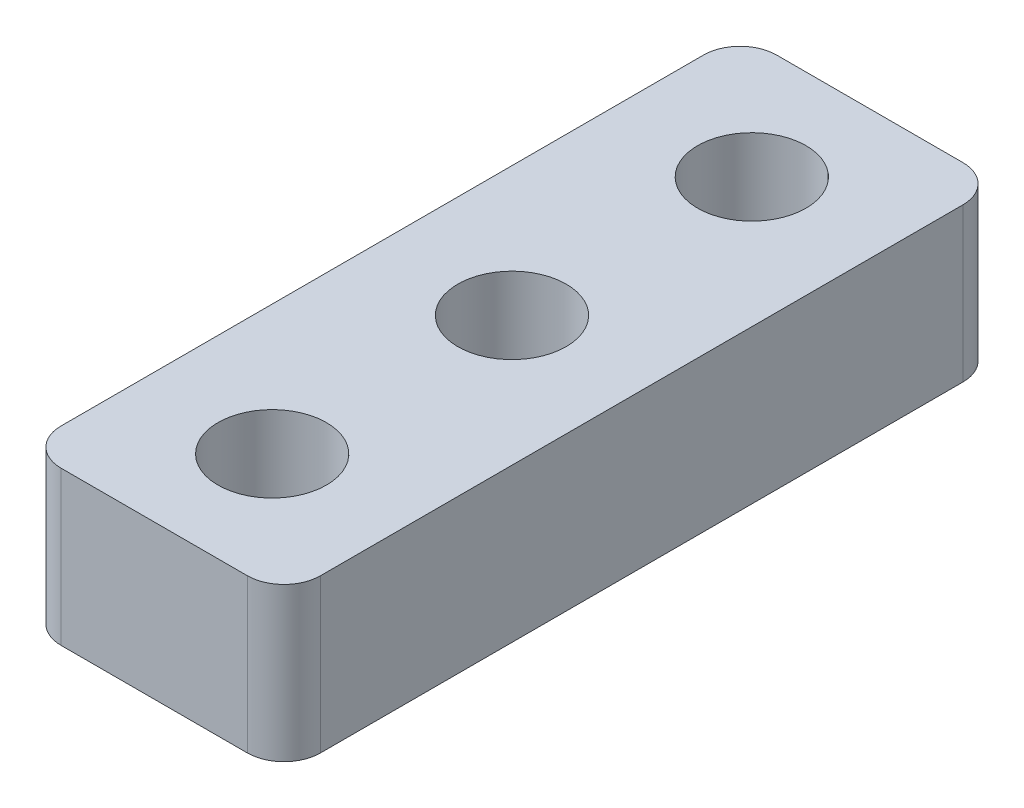
SolidWorks part; units mm, degrees
ref_plane "Front" through (0, 0, 0) normal (0, 0, 1) x (1, 0, 0)
ref_plane "Top" through (0, 0, 0) normal (0, 1, 0) x (1, 0, 0)
ref_plane "Right" through (0, 0, 0) normal (1, 0, 0) x (0, 0, -1)
sketch "Sketch1" plane through (0, 0, 0) normal (0, 0, 1) x (1, 0, 0)
  line L0 (0, 0) -> (0, 3.2004)
  line L1 (5.409, 3.7004) -> (0, 3.7004) construction
  line L2 (5.409, 3.7004) -> (5.409, 0) construction
  line L5 (2.7045, 3.7004) -> (2.7045, 0) construction
  line L10 (0, 3.2004) -> (5.409, 3.2004)
  line L15 (5.409, 3.7004) -> (5.409, 0) construction
  line L20 (0, 0) -> (5.409, 0)
  line L25 (5.409, 3.2004) -> (5.409, 0)
  line L30 (0, 3.7004) -> (0, 0) construction
  dimension "D1" = 5.409
  dimension "D2" = 3.2004
  dimension "D3" = 0.5
extrude "Boss-Extrude1" add sketch "Sketch1" along normal mid plane 14.92
sketch "Sketch3" plane through (0, 0, 0) normal (0, -1, 0) x (1, 0, 0)
  line L0 (0, 0) -> (5.409, 0) construction
  line L3 (0, 7.46) -> (0, -7.46) construction
  line L6 (2.7045, 5) -> (2.7045, -5) construction
  line L7 (5.409, 7.46) -> (5.409, -7.46) construction
  circle A0 centre (2.7045, 5) radius 1.1303
  circle A1 centre (2.7045, -5) radius 1.1303
  circle A2 centre (2.7045, 0) radius 1.1303
  point P8 (2.7045, 0)
  dimension "D1" = 2.2606
  dimension "D2" = 10
extrude "Cut-Extrude1" cut sketch "Sketch3" against normal up to surface (3.2004 mm away) up to face at (2.7045, 3.2004, 0)
fillet "Fillet1" radius 0.762 4 edges at (0, 1.6002, -7.46) (5.409, 1.6002, -7.46) (5.409, 1.6002, 7.46) (0, 1.6002, 7.46)
sketch "Sketch4" plane through (5.409, 0, 0) normal (1, 0, 0) x (0, 0, -1)
  line L0 (0, 3.2004) -> (0, 0) construction
  line L1 (-6.698, 3.2004) -> (6.698, 3.2004) construction
  line L2 (-6.698, 0) -> (6.698, 0) construction
sketch "Sketch5" plane through (0, 0, 7.46) normal (0, 0, 1) x (1, 0, 0)
  line L0 (2.7045, 3.2004) -> (2.7045, 0) construction
  line L1 (4.647, 3.2004) -> (0.762, 3.2004) construction
  line L2 (0.762, 0) -> (4.647, 0) construction
